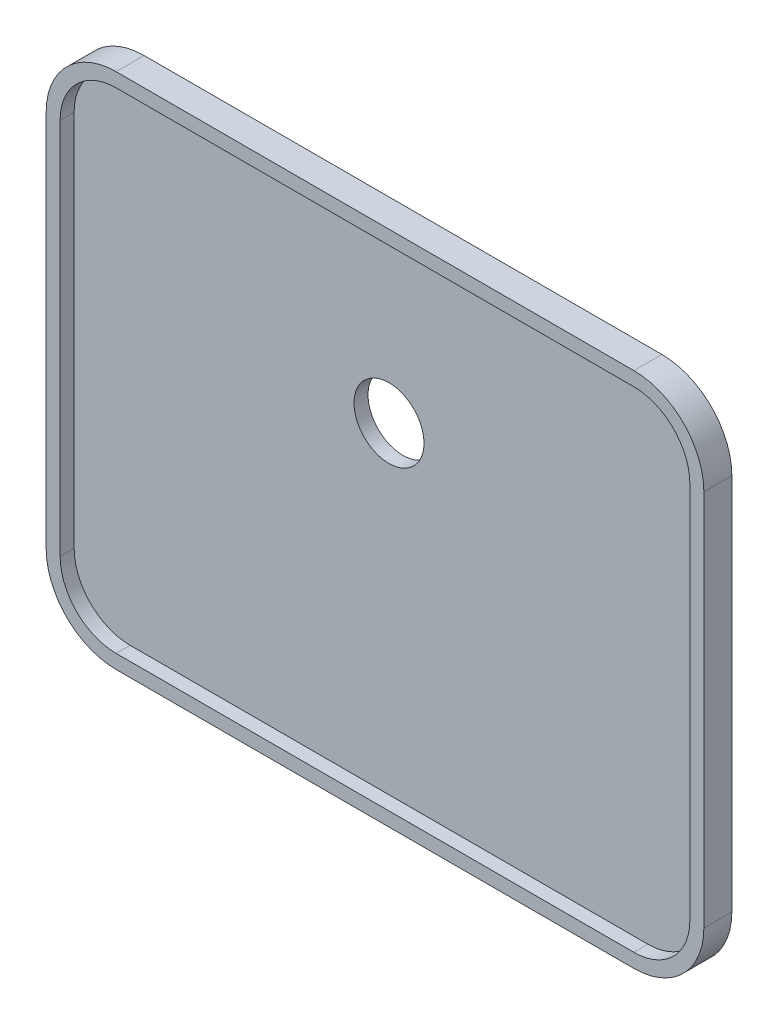
SolidWorks part; units mm, degrees
ref_plane "Ebene vorne" through (0, 0, 0) normal (0, 0, 1) x (1, 0, 0)
ref_plane "Ebene oben" through (0, 0, 0) normal (0, 1, 0) x (1, 0, 0)
ref_plane "Ebene rechts" through (0, 0, 0) normal (1, 0, 0) x (0, 0, -1)
sketch "Skizze1" plane through (0, 0, 0) normal (0, 0, 1) x (1, 0, 0)
  line L0 (-0.3303, 95.0936) -> (369.6697, 95.0936)
  line L1 (-0.3303, 85.0936) -> (369.6697, 85.0936)
  line L2 (-40.3303, 45.0936) -> (-40.3303, -224.9064)
  line L3 (-0.3303, -264.9064) -> (369.6697, -264.9064)
  line L4 (409.6697, 45.0936) -> (409.6697, -224.9064)
  line L5 (419.6697, 45.0936) -> (419.6697, -224.9064)
  line L6 (-0.3303, -274.9064) -> (369.6697, -274.9064)
  line L7 (-50.3303, 45.0936) -> (-50.3303, -224.9064)
  arc A0 (-40.3303, -224.9064) -> (-0.3303, -264.9064) centre (-0.3303, -224.9064) ccw
  arc A1 (369.6697, -264.9064) -> (409.6697, -224.9064) centre (369.6697, -224.9064) ccw
  arc A2 (409.6697, 45.0936) -> (369.6697, 85.0936) centre (369.6697, 45.0936) ccw
  arc A3 (-40.3303, 45.0936) -> (-0.3303, 85.0936) centre (-0.3303, 45.0936) cw
  arc A4 (419.6697, 45.0936) -> (369.6697, 95.0936) centre (369.6697, 45.0936) ccw
  arc A5 (369.6697, -274.9064) -> (419.6697, -224.9064) centre (369.6697, -224.9064) ccw
  arc A6 (-50.3303, -224.9064) -> (-0.3303, -274.9064) centre (-0.3303, -224.9064) ccw
  arc A7 (-50.3303, 45.0936) -> (-0.3303, 95.0936) centre (-0.3303, 45.0936) cw
  point P6 (-40.3303, -264.9064)
  point P11 (409.6697, 85.0936)
  point P14 (-40.3303, 85.0936)
  dimension "D3" = 40
  dimension "D1" = 450
  dimension "D2" = 350
  dimension "D4" = 10
extrude "Aufsatz-Linear austragen1" add sketch "Skizze1" along normal blind 20
sketch "Skizze2" plane through (0, 0, 0) normal (0, 0, 1) x (1, 0, 0)
  line L1 (-0.3303, -264.9064) -> (369.6697, -264.9064)
  line L2 (-40.3303, -224.9064) -> (-40.3303, 45.0936)
  line L3 (-0.3303, 85.0936) -> (369.6697, 85.0936)
  line L4 (409.6697, -224.9064) -> (409.6697, 45.0936)
  arc A0 (-40.3303, -224.9064) -> (-0.3303, -264.9064) centre (-0.3303, -224.9064) ccw
  arc A1 (409.6697, -224.9064) -> (369.6697, -264.9064) centre (369.6697, -224.9064) cw
  arc A2 (409.6697, 45.0936) -> (369.6697, 85.0936) centre (369.6697, 45.0936) ccw
  arc A3 (-0.3303, 85.0936) -> (-40.3303, 45.0936) centre (-0.3303, 45.0936) ccw
  dimension "D1" = 40
extrude "Aufsatz-Linear austragen2" add sketch "Skizze2" along normal blind 10
sketch "Skizze3" plane through (0, 0, 0) normal (0, 0, 1) x (1, 0, 0)
  line L1 (369.6697, 85.0936) -> (-0.3303, 85.0936) construction
  circle A0 centre (184.6697, -34.9064) radius 25
  point P5 (184.6697, 85.0936)
  dimension "D1" = 225
  dimension "D2" = 120
extrude "Schnitt-Linear austragen1" cut sketch "Skizze3" along normal blind 15
ref_plane "Ebene1" through (184.6697, 0, 0) normal (-1, 0, 0) x (0, 0, 1)
sketch "Skizze6" plane through (184.6697, 0, 0) normal (-1, 0, 0) x (0, 0, 1)
  line L0 (10, -59.9064) -> (20, -264.9064)
  line L1 (20, -264.9064) -> (10, -264.9064)
  line L2 (10, -264.9064) -> (10, -59.9064)
sketch "Skizze7" plane through (184.6697, 0, 0) normal (-1, 0, 0) x (0, 0, 1)
  line L0 (20, 85.0936) -> (10, 85.0936)
  line L1 (10, 85.0936) -> (10, -9.9064)
  line L2 (10, -9.9064) -> (20, 85.0936)
sketch "Skizze8" plane through (0, 0, 0) normal (0, 0, 1) x (1, 0, 0)
  line L0 (184.6697, -34.9064) -> (-84.2974, -34.9064) construction
ref_plane "Ebene2" through (0, -34.9064, 0) normal (0, -1, 0) x (1, 0, 0)
sketch "Skizze9" plane through (0, -34.9064, 0) normal (0, -1, 0) x (1, 0, 0)
  line L0 (-40.3303, 20) -> (-40.3303, 10)
  line L1 (-40.3303, 10) -> (159.6697, 10)
  line L2 (159.6697, 10) -> (-40.3303, 20)
sketch "Skizze11" plane through (0, -34.9064, 0) normal (0, -1, 0) x (1, 0, 0)
  line L0 (409.6697, 20) -> (209.6697, 10)
  line L1 (209.6697, 10) -> (409.6697, 10)
  line L2 (409.6697, 20) -> (409.6697, 10) construction
  line L3 (409.6697, 10) -> (409.6697, 20)
ref_plane "Ebene3" through (0, 0, 20) normal (0, 0, 1) x (1, 0, 0)
sketch "Skizze12" plane through (0, 0, 20) normal (0, 0, 1) x (1, 0, 0)
  line L1 (-0.3303, 85.0936) -> (369.6697, 85.0936)
  line L2 (-40.3303, 45.0936) -> (-40.3303, -224.9064)
  line L3 (-0.3303, -264.9064) -> (369.6697, -264.9064)
  line L4 (409.6697, 45.0936) -> (409.6697, -224.9064)
  arc A0 (-40.3303, -224.9064) -> (-0.3303, -264.9064) centre (-0.3303, -224.9064) ccw
  arc A1 (369.6697, -264.9064) -> (409.6697, -224.9064) centre (369.6697, -224.9064) ccw
  arc A2 (409.6697, 45.0936) -> (369.6697, 85.0936) centre (369.6697, 45.0936) ccw
  arc A3 (-40.3303, 45.0936) -> (-0.3303, 85.0936) centre (-0.3303, 45.0936) cw
  dimension "D1" = 40
